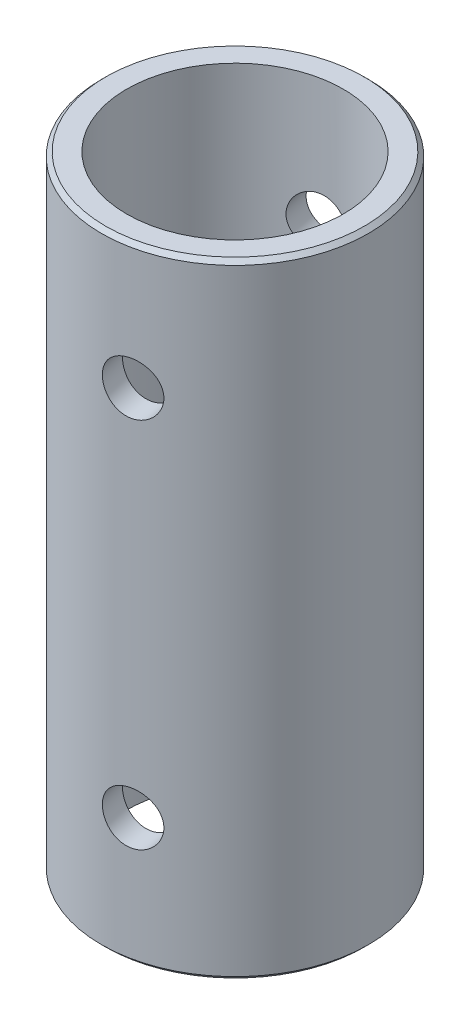
SolidWorks part; units mm, degrees
ref_plane "Front Plane" through (0, 0, 0) normal (0, 0, 1) x (1, 0, 0)
ref_plane "Top Plane" through (0, 0, 0) normal (0, 1, 0) x (1, 0, 0)
ref_plane "Right Plane" through (0, 0, 0) normal (1, 0, 0) x (0, 0, -1)
sketch "Sketch1" plane through (0, 0, 0) normal (0, 1, 0) x (1, 0, 0)
  circle A0 centre (0, 0) radius 7.94
  circle A1 centre (0, 0) radius 6.44
  dimension "D1" = 15.88
  dimension "D2" = 1.5
extrude "Boss-Extrude1" add sketch "Sketch1" along normal blind 37.13
chamfer "Chamfer1" distance 0.25 angle 45 2 edges at (0, 0, 7.94) (0, 37.13, 7.94)
sketch "Sketch2" plane through (-1.1785, 0, -5.7301) normal (-0.2015, 0, -0.9795) x (-0.9795, 0, 0.2015)
  circle A0 centre (0, 7.5) radius 1.55 construction
  circle A1 centre (0, 7.5) radius 1.55
  spline S0 degree 3 poles (0.5771, 28.1915) (3.4541, 29.346) (2.2995, 32.223) (-0.5775, 31.0685) (-3.4544, 29.914) (-2.2999, 27.037) (0.5771, 28.1915) (3.4541, 29.346) (2.2995, 32.223) knots -0.5 0 0 0 0.5 0.5 0.5 1 1 1 1.5 1.5 1.5 weights 1 0.333333 0.333333 1 0.333333 0.333333 1 0.333333 0.333333 only from (0.5771, 28.1915) to (0.5771, 28.1915) construction
  spline S1 degree 3 poles (0.5771, 28.1915) (3.4541, 29.346) (2.2995, 32.223) (-0.5775, 31.0685) (-3.4544, 29.914) (-2.2999, 27.037) (0.5771, 28.1915) (3.4541, 29.346) (2.2995, 32.223) knots -0.5 0 0 0 0.5 0.5 0.5 1 1 1 1.5 1.5 1.5 weights 1 0.333333 0.333333 1 0.333333 0.333333 1 0.333333 0.333333 only from (0.5771, 28.1915) to (0.5771, 28.1915)
extrude "Cut-Extrude1" cut sketch "Sketch2" against normal through all and the other way through all
